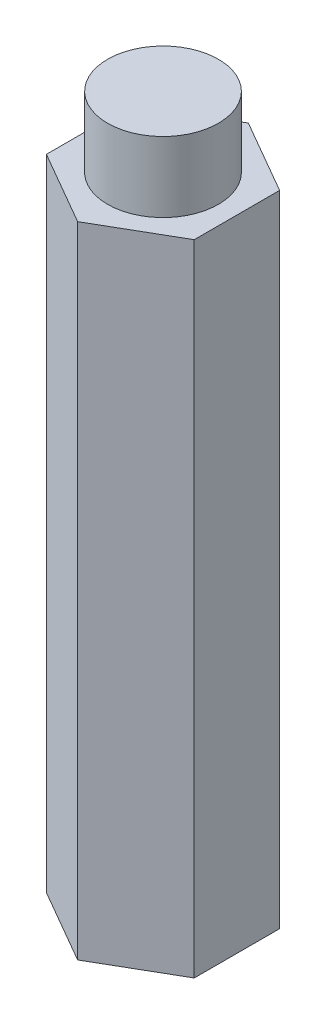
SolidWorks part; units mm, degrees
material "7075-T6 (SN)"
ref_plane "Front Plane" through (0, 0, 0) normal (0, 0, 1) x (1, 0, 0)
ref_plane "Top Plane" through (0, 0, 0) normal (0, 1, 0) x (1, 0, 0)
ref_plane "Right Plane" through (0, 0, 0) normal (1, 0, 0) x (0, 0, -1)
sketch "Sketch1" plane through (0, 0, 0) normal (0, 1, 0) x (1, 0, 0)
  line L1 (6.35, -3.6662) -> (6.35, 3.6662)
  line L2 (6.35, 3.6662) -> (0, 7.3323)
  line L3 (0, 7.3323) -> (-6.35, 3.6662)
  line L4 (-6.35, 3.6662) -> (-6.35, -3.6662)
  line L5 (-6.35, -3.6662) -> (0, -7.3323)
  line L6 (0, -7.3323) -> (6.35, -3.6662)
  circle A0 centre (0, 0) radius 6.35 construction
  dimension "D1" = 12.7
extrude "Boss-Extrude1" add sketch "Sketch1" along normal blind 54.9275
sketch "Sketch2" plane through (0, 0, 0) normal (0, 1, 0) x (1, 0, 0)
  circle A0 centre (0, 0) radius 4.7625
  dimension "D1" = 9.525
extrude "Boss-Extrude2" add sketch "Sketch2" along normal blind 60.96
